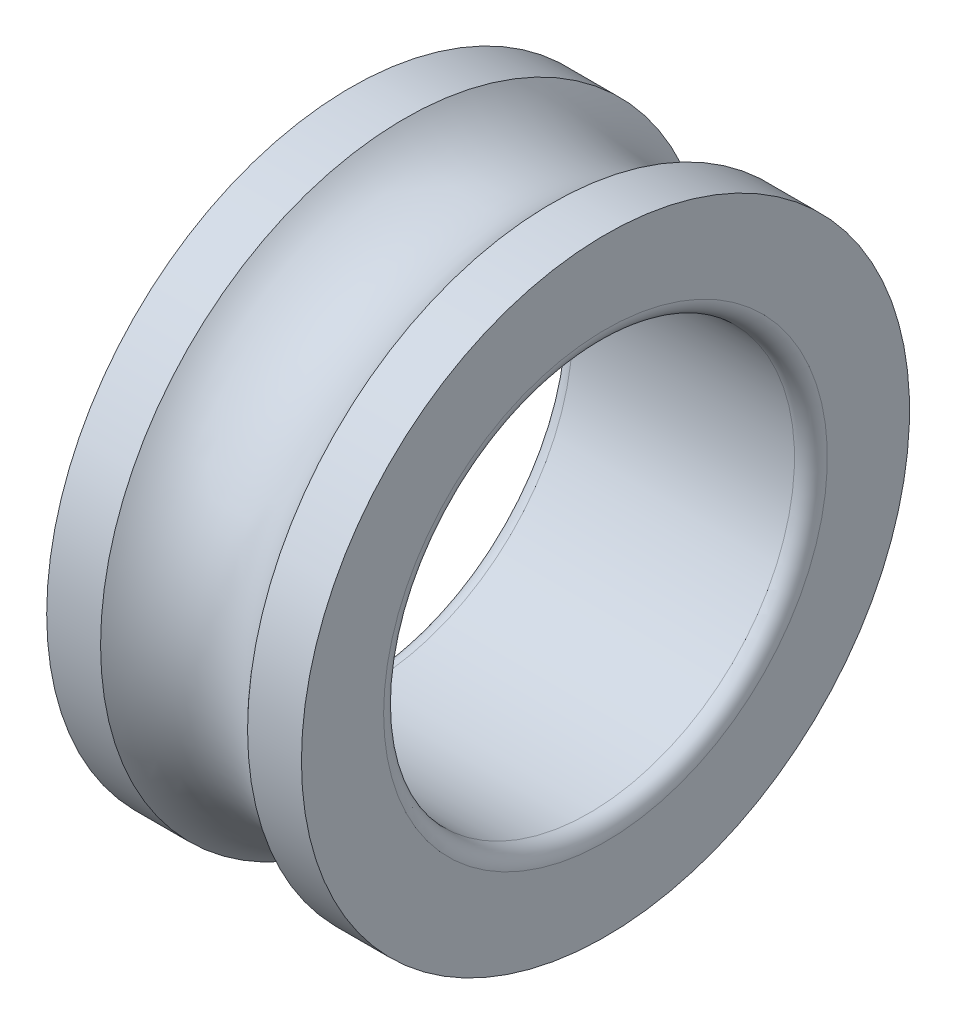
SolidWorks part; units mm, degrees
ref_plane "Front Plane" through (0, 0, 0) normal (0, 0, 1) x (1, 0, 0)
ref_plane "Top Plane" through (0, 0, 0) normal (0, 1, 0) x (1, 0, 0)
ref_plane "Right Plane" through (0, 0, 0) normal (1, 0, 0) x (0, 0, -1)
sketch "Sketch1" plane through (0, 0, 0) normal (0, 0, 1) x (1, 0, 0)
  line L0 (-15.5, 0) -> (25.9722, 0) construction
  line L1 (0, 0.93) -> (0, 51.2878) construction
  line L2 (13.5, 25) -> (-13.5, 25)
  line L3 (15.5, 27) -> (15.5, 37)
  line L4 (15.5, 37) -> (8.9443, 37)
  line L5 (-15.5, 27) -> (-15.5, 37)
  line L6 (15.5, 25) -> (-15.5, 37) construction
  line L7 (15.5, 37) -> (-15.5, 25) construction
  line L8 (-8.9443, 37) -> (-15.5, 37)
  arc A0 (8.9443, 37) -> (-8.9443, 37) centre (0, 45) cw
  arc A1 (13.5, 25) -> (15.5, 27) centre (13.5, 27) ccw
  arc A2 (-13.5, 25) -> (-15.5, 27) centre (-13.5, 27) cw
  point P3 (0, 31)
  dimension "D5" = 12
  dimension "D6" = 2
  dimension "D1" = 25
  dimension "D2" = 31
  dimension "D3" = 37
  dimension "D4" = 8
revolve "Revolve1" add sketch "Sketch1" angle 360 about L0
